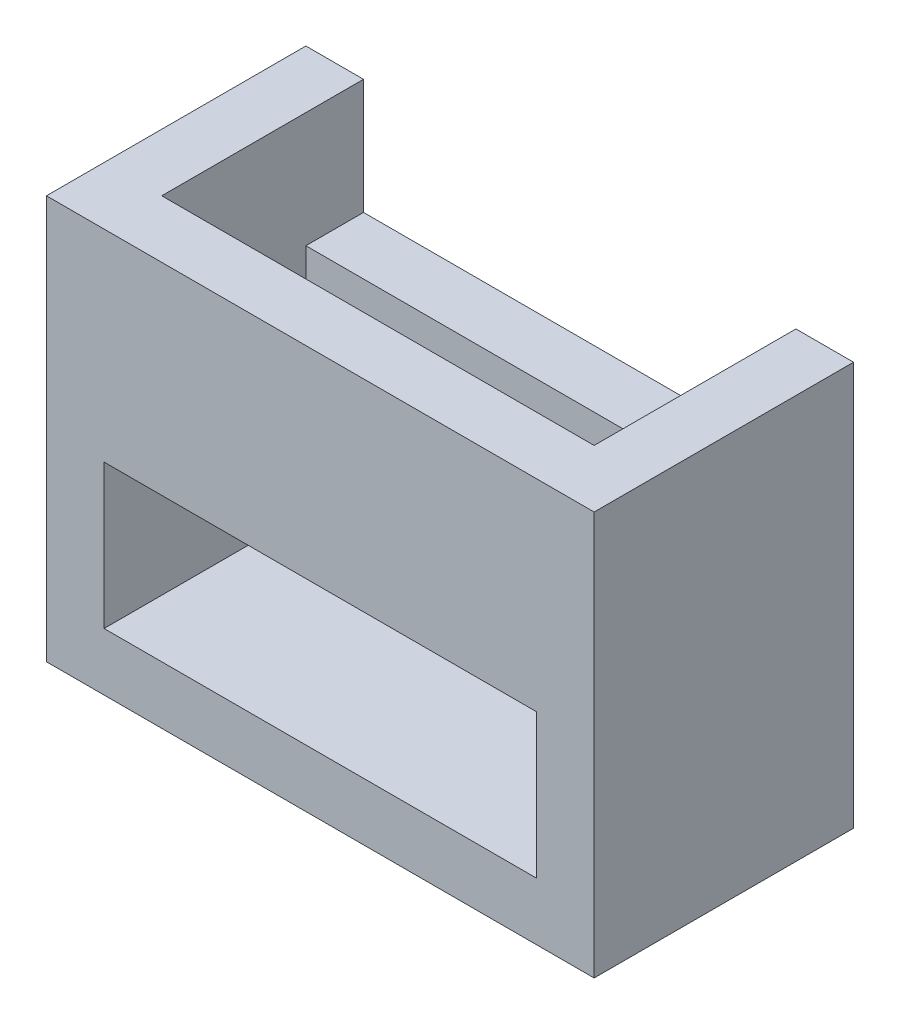
SolidWorks part; units mm, degrees
ref_plane "Front Plane" through (0, 0, 0) normal (0, 0, 1) x (1, 0, 0)
ref_plane "Top Plane" through (0, 0, 0) normal (0, 1, 0) x (1, 0, 0)
ref_plane "Right Plane" through (0, 0, 0) normal (1, 0, 0) x (0, 0, -1)
sketch "Sketch2" plane through (0, 0, 0) normal (0, 0, 1) x (1, 0, 0)
  line L1 (-9.5, 7) -> (9.5, 7)
  line L2 (-9.5, 7) -> (-9.5, -7)
  line L3 (-9.5, -7) -> (9.5, -7)
  line L4 (9.5, 7) -> (9.5, -7)
  line L5 (-9.5, 7) -> (9.5, -7) construction
  line L6 (-9.5, -7) -> (9.5, 7) construction
  point P0 (0, 0)
  dimension "D1" = 19
  dimension "D2" = 14
extrude "Boss-Extrude1" add sketch "Sketch2" along normal blind 9
sketch "Sketch3" plane through (0, 0, 9) normal (0, 0, 1) x (1, 0, 0)
  line L0 (-9.5, -7) -> (-7.5, -7)
  line L1 (-9.5, -7) -> (9.5, -7) construction
  line L2 (-9.5, -7) -> (-9.5, -5)
  line L3 (-9.5, 7) -> (-9.5, -7) construction
  line L4 (-9.5, -5) -> (-9.5, 0)
  line L6 (-7.5, -5) -> (7.5, -5)
  line L7 (-7.5, -5) -> (-7.5, 0)
  line L8 (-7.5, 0) -> (7.5, 0)
  line L9 (7.5, -5) -> (7.5, 0)
  dimension "D1" = 2
  dimension "D2" = 2
  dimension "D3" = 5
  dimension "D4" = 15
extrude "Cut-Extrude1" cut sketch "Sketch3" against normal blind 5 contours L6 L9 L8 L7
sketch "Sketch6" plane through (0, 7, 0) normal (0, 1, 0) x (1, 0, 0)
  line L0 (-9.5, -9) -> (-9.5, -7)
  line L1 (-9.5, -9) -> (-9.5, 0) construction
  line L2 (-9.5, -9) -> (-7.5, -9)
  line L3 (9.5, -9) -> (-9.5, -9) construction
  line L4 (9.5, 0) -> (7.5, 0)
  line L5 (9.5, 0) -> (-9.5, 0) construction
  line L6 (9.5, 0) -> (9.5, -2)
  line L7 (9.5, -9) -> (9.5, 0) construction
  line L9 (-7.5, -7) -> (7.5, -7)
  line L10 (-7.5, -7) -> (-7.5, 0)
  line L11 (-7.5, 0) -> (7.5, 0)
  line L12 (7.5, -7) -> (7.5, 0)
  line M5 (9.5, 0) -> (-9.5, 0)
  dimension "D1" = 2
  dimension "D2" = 2
  dimension "D3" = 2
  dimension "D4" = 2
extrude "Cut-Extrude3" cut sketch "Sketch6" against normal blind 4 contours L9 L12 L10 M5
sketch "Sketch7" plane through (0, 3, 0) normal (0, 1, 0) x (1, 0, 0)
  line L0 (7.5, 0) -> (7.5, -2)
  line L1 (7.5, -7) -> (7.5, 0) construction
  line L2 (-7.5, -7) -> (-7.5, 0) construction
  line L3 (7.5, -2) -> (-7.5, -2)
  line L4 (7.5, -2) -> (7.5, -7)
  line L5 (7.5, -7) -> (-7.5, -7)
  line L6 (-7.5, -2) -> (-7.5, -7)
  line L7 (-7.5, -7) -> (7.5, -7) construction
  line M2 (-7.5, -7) -> (7.5, -7)
  line M3 (7.5, -7) -> (7.5, 0)
  line M5 (-7.5, 0) -> (-7.5, -7)
  dimension "D1" = 2
extrude "Cut-Extrude4" cut sketch "Sketch7" against normal blind 4 contours L3 M3 M5 M2
